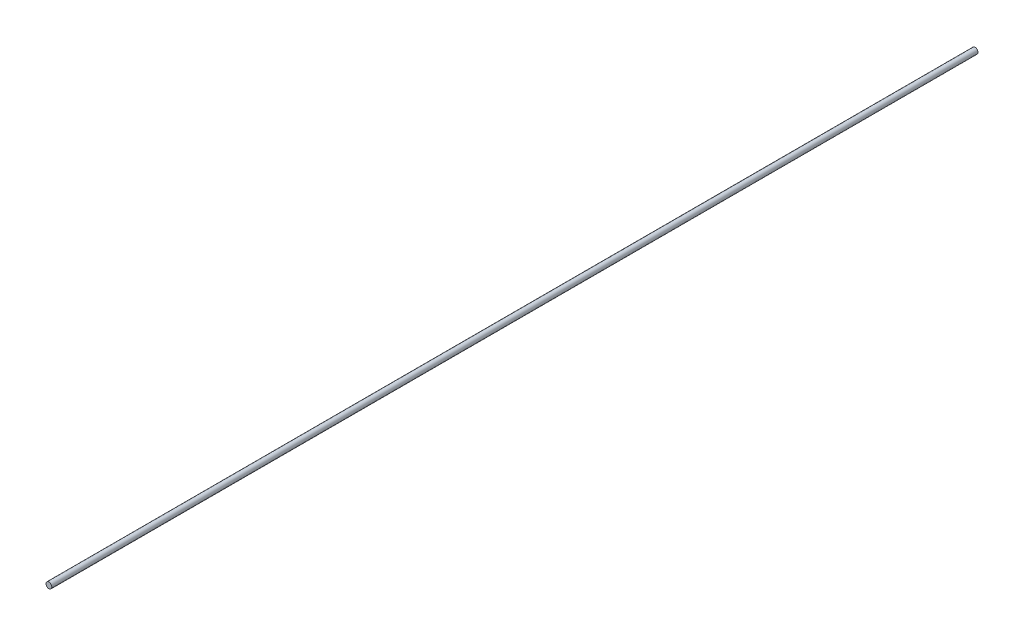
SolidWorks part; units mm, degrees
ref_plane "Plan de face" through (0, 0, 0) normal (0, 0, 1) x (1, 0, 0)
ref_plane "Plan de dessus" through (0, 0, 0) normal (0, 1, 0) x (1, 0, 0)
ref_plane "Plan de droite" through (0, 0, 0) normal (1, 0, 0) x (0, 0, -1)
sketch "Esquisse1" plane through (0, 0, 0) normal (0, 0, 1) x (1, 0, 0)
  circle A0 centre (0, 0) radius 3
  dimension "D1" = 6
extrude "Boss.-Extru.1" add sketch "Esquisse1" along normal blind 956.16
